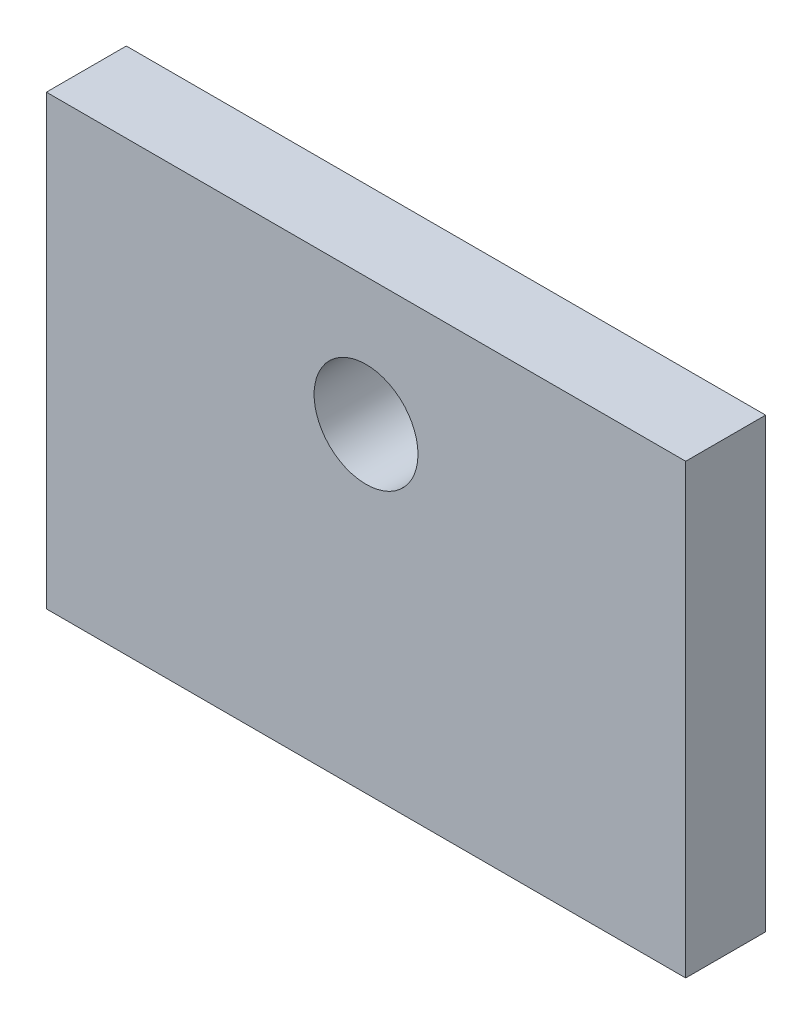
SolidWorks part; units mm, degrees
ref_plane "前视基准面" through (0, 0, 0) normal (0, 0, 1) x (1, 0, 0)
ref_plane "上视基准面" through (0, 0, 0) normal (0, 1, 0) x (1, 0, 0)
ref_plane "右视基准面" through (0, 0, 0) normal (1, 0, 0) x (0, 0, -1)
sketch "草图1" plane through (0, 0, 0) normal (0, 0, 1) x (1, 0, 0)
  line L0 (-57.1787, 12.5893) -> (75.2351, 12.5893) construction
  line L1 (-36.1129, 28.5893) -> (43.8871, 28.5893)
  line L2 (-36.1129, 28.5893) -> (-36.1129, -27.4107)
  line L3 (-36.1129, -27.4107) -> (43.8871, -27.4107)
  line L4 (43.8871, 28.5893) -> (43.8871, -27.4107)
  line L5 (3.8871, -59.9373) -> (3.8871, 97.0533) construction
  circle A0 centre (3.8871, 12.5893) radius 6.5
  dimension "D4" = 13
  dimension "D1" = 80
  dimension "D2" = 56
  dimension "D3" = 40
extrude "凸台-拉伸1" add sketch "草图1" along normal blind 10
